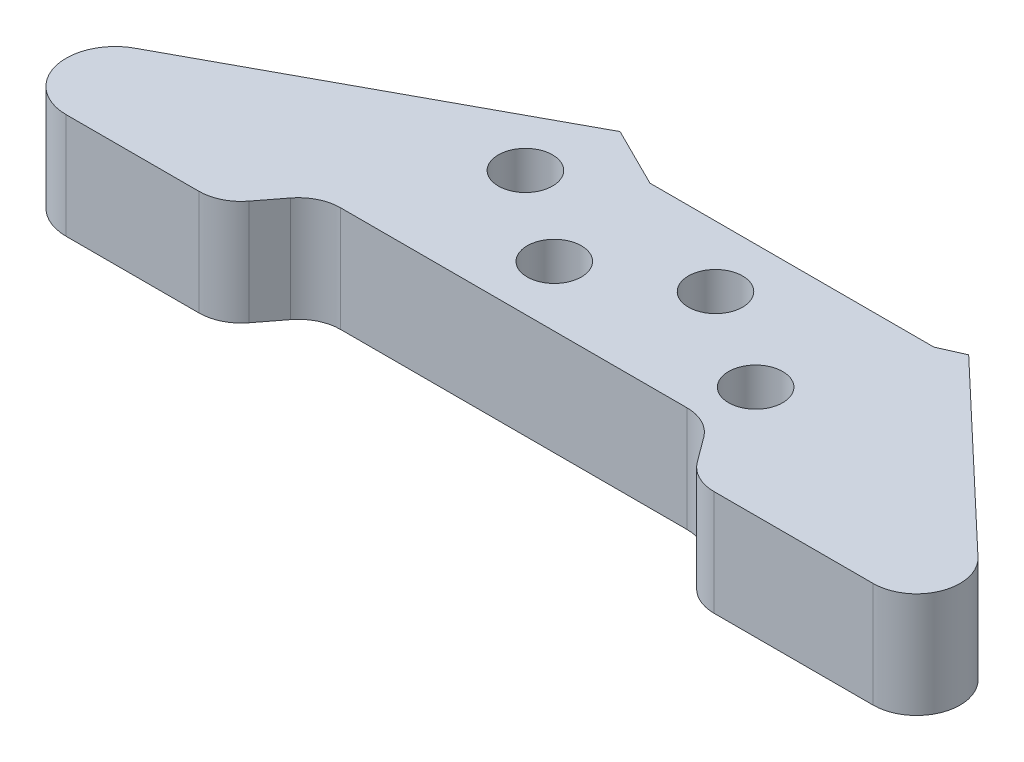
SolidWorks part; units mm, degrees
material "PE High Density"
ref_plane "Front Plane" through (0, 0, 0) normal (0, 0, 1) x (1, 0, 0)
ref_plane "Top Plane" through (0, 0, 0) normal (0, 1, 0) x (1, 0, 0)
ref_plane "Right Plane" through (0, 0, 0) normal (1, 0, 0) x (0, 0, -1)
sketch "Sketch1" plane through (0, 0, 0) normal (0, 1, 0) x (1, 0, 0)
  line L0 (98.733, -68.9858) -> (100.9426, -71.978)
  line L1 (52.8997, -66.9235) -> (94.6465, -66.9235)
  line L2 (61.7924, -42.1316) -> (24.0383, -62.5632)
  line L3 (26.6541, -73.7386) -> (42.6586, -73.7386)
  line L4 (46.6879, -71.7523) -> (48.8703, -68.9098)
  line L5 (61.7924, -42.1316) -> (68.9774, -45.7135)
  line L6 (106.0943, -44.4268) -> (127.8024, -65.01)
  line L7 (124.2019, -74.0403) -> (105.0291, -74.0403)
  line L8 (68.9774, -45.7135) -> (103.1982, -45.7135)
  line L9 (103.1982, -45.7135) -> (106.0943, -44.4268)
  arc A0 (94.6465, -66.9235) -> (98.733, -68.9858) centre (94.6465, -72.0035) cw
  arc A1 (52.8997, -66.9235) -> (48.8703, -68.9098) centre (52.8997, -72.0035) ccw
  arc A2 (42.6586, -73.7386) -> (46.6879, -71.7523) centre (42.6586, -68.6586) ccw
  arc A3 (42.6586, -73.7386) -> (44.2181, -73.4933) centre (42.6586, -68.6586) ccw construction
  arc A4 (24.0383, -62.5632) -> (26.6541, -73.7386) centre (26.6541, -67.8448) ccw
  circle A5 centre (60.1502, -51.8912) radius 3.2639
  circle A6 centre (71.3764, -59.6418) radius 3.2639
  arc A7 (127.8024, -65.01) -> (124.2019, -74.0403) centre (124.2019, -68.8074) cw
  arc A8 (100.9426, -71.978) -> (105.0291, -74.0403) centre (105.0291, -68.9603) ccw
  arc A9 (124.2019, -74.0403) -> (127.8024, -65.01) centre (124.2019, -68.8074) ccw construction
  circle A10 centre (84.2377, -53.0771) radius 3.2639
  circle A11 centre (96.6303, -60.6336) radius 3.2639
  arc A13 (24.0383, -62.5632) -> (22.2281, -71.7367) centre (26.6541, -67.8448) ccw construction
  point P0 (0, 0)
  dimension "D1" = 6.5278
extrude "Boss-Extrude1" add sketch "Sketch1" along normal blind 12.7
sketch "Sketch2" [suppressed] plane through (0, 0, 0) normal (0, -1, 0) x (1, 0, 0)
  line L0 (61.7924, 42.1316) -> (24.0383, 62.5632) construction
  line L1 (65.8959, 48.7818) -> (65.7159, 55.3124)
  line L2 (65.7159, 55.3124) -> (59.9702, 58.4218)
  line L3 (59.9702, 58.4218) -> (54.4045, 55.0006)
  line L4 (54.4045, 55.0006) -> (54.5845, 48.47)
  line L5 (54.5845, 48.47) -> (60.3302, 45.3606)
  line L6 (60.3302, 45.3606) -> (65.8959, 48.7818)
  line L7 (90.7703, 53.1638) -> (87.4289, 58.7778)
  line L8 (87.4289, 58.7778) -> (80.8963, 58.6911)
  line L9 (80.8963, 58.6911) -> (77.7052, 52.9903)
  line L10 (77.7052, 52.9903) -> (81.0466, 47.3764)
  line L11 (81.0466, 47.3764) -> (87.5791, 47.4631)
  line L12 (87.5791, 47.4631) -> (90.7703, 53.1638)
  circle A0 centre (60.1502, 51.8912) radius 5.6579 construction
  circle A1 centre (84.2377, 53.0771) radius 5.6579 construction
  dimension "D1" = 11.3157
extrude "Cut-Extrude1" [suppressed] cut sketch "Sketch2" against normal through all
chamfer "Chamfer1" [suppressed] distance 4.0894 angle 41
